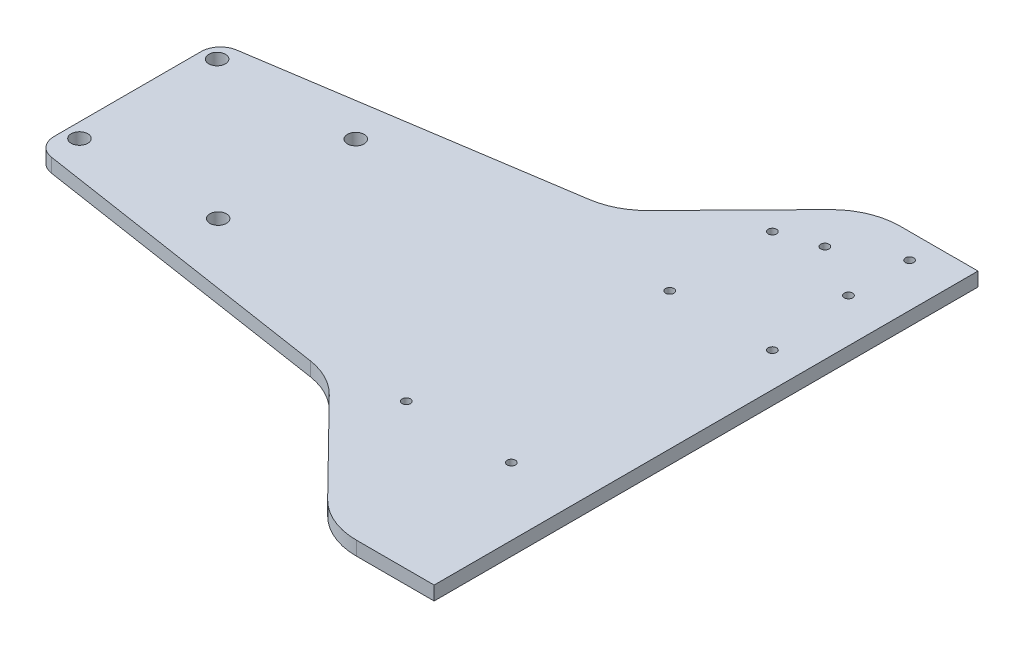
SolidWorks part; units mm, degrees
material "Plastique personnalisé"
ref_plane "Plan de face" through (0, 0, 0) normal (0, 0, 1) x (1, 0, 0)
ref_plane "Plan de dessus" through (0, 0, 0) normal (0, 1, 0) x (1, 0, 0)
ref_plane "Plan de droite" through (0, 0, 0) normal (1, 0, 0) x (0, 0, -1)
sketch "Esquisse1" plane through (0, 0, 0) normal (0, 1, 0) x (1, 0, 0)
  line L0 (0, 0) -> (200, 0) construction
  line L1 (200, -98) -> (200, 98) construction
  line L2 (0, -32.5) -> (0, 32.5) construction
  line L4 (200, 98) -> (180.4869, 98)
  line L5 (162.6514, 90.5184) -> (130.2275, 57.5077)
  line L6 (0, 19.6247) -> (0, -19.6247)
  line L7 (200, 98) -> (200, -98)
  line L8 (200, -98) -> (180.4869, -98)
  line L9 (162.6514, -90.5184) -> (130.2275, -57.5077)
  line L11 (116.1812, -50.3149) -> (0, -32.5)
  line L12 (0, -19.6247) -> (0, -32.5)
  line L13 (116.1812, 50.3149) -> (0, 32.5)
  line L14 (0, 32.5) -> (0, 19.6247)
  arc A0 (116.1812, 50.3149) -> (130.2275, 57.5077) centre (112.392, 75.0261) ccw
  arc A1 (180.4869, 98) -> (162.6514, 90.5184) centre (180.4869, 73) ccw
  arc A3 (180.4869, -98) -> (162.6514, -90.5184) centre (180.4869, -73) cw
  arc A4 (116.1812, -50.3149) -> (130.2275, -57.5077) centre (112.392, -75.0261) cw
  point P13 (170, 98)
  dimension "D5" = 25
  dimension "D1" = 200
  dimension "D2" = 98
  dimension "D3" = 32.5
  dimension "D4" = 30
extrude "Boss.-Extru.1" add sketch "Esquisse1" along normal blind 5
fillet "Congé3" radius 7 2 edges at (0, 2.5, 32.5) (0, 2.5, -32.5)
sketch "Esquisse3" plane through (0, 5, 0) normal (0, 1, 0) x (1, 0, 0)
  circle A0 centre (5.2281, -22.5421) radius 3
  circle A1 centre (5.2281, 27.0588) radius 3
  circle A2 centre (55.2084, -22.5421) radius 3
  circle A3 centre (55.2084, 27.0588) radius 3
  dimension "D1" = 6
  dimension "D2" = 6
  dimension "D3" = 6
  dimension "D4" = 6
extrude "Enlèv. mat.-Extru.1" cut sketch "Esquisse3" against normal blind 5
sketch "Esquisse8" plane through (0, 5, 0) normal (0, 1, 0) x (1, 0, 0)
  circle A0 centre (196.1489, 36.2746) radius 1.5
  circle A2 centre (159.1489, 73.2746) radius 1.5
  circle A3 centre (159.1489, 36.2746) radius 1.5
extrude "Enlèv. mat.-Extru.5" cut sketch "Esquisse8" against normal blind 10
ref_plane "section" through (100, 0, 0) normal (1, 0, 0) x (0, 0, -1)
sketch "Esquisse11" plane through (0, 5, 0) normal (0, 1, 0) x (1, 0, 0)
  circle A0 centre (184.1991, -45.8698) radius 1.5
  circle A1 centre (146.1501, -45.6605) radius 1.5
extrude "Enlèv. mat.-Extru.7" cut sketch "Esquisse11" against normal blind 10
sketch "Esquisse12" plane through (0, 0, 0) normal (0, -1, 0) x (-1, 0, 0)
  line L1 (-200, -98) -> (-208.5132, -98)
  line L2 (-200, -98) -> (-200, 98.0231)
  line L3 (-200, 98.0231) -> (-208.5132, 98.0231)
  line L4 (-208.5132, -98) -> (-208.5132, 98.0231)
extrude "Boss.-Extru.2" add sketch "Esquisse12" against normal blind 5
sketch "Esquisse13" plane through (0, 5, 0) normal (0, 1, 0) x (1, 0, 0)
  circle A0 centre (192.8013, 89.0722) radius 1.4967
  circle A1 centre (173.2691, 78.0588) radius 1.5018
  circle A2 centre (192.8013, 67.0455) radius 1.5003
extrude "Enlèv. mat.-Extru.8" cut sketch "Esquisse13" against normal blind 10
